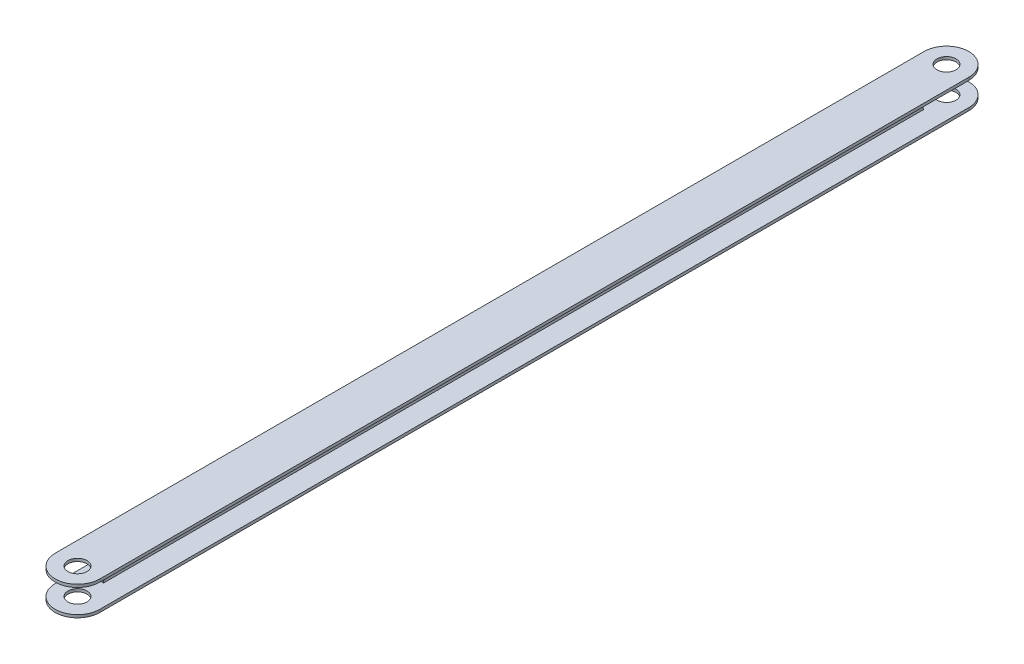
SolidWorks part; units mm, degrees
ref_plane "Front Plane" through (0, 0, 0) normal (0, 0, 1) x (1, 0, 0)
ref_plane "Top Plane" through (0, 0, 0) normal (0, 1, 0) x (1, 0, 0)
ref_plane "Right Plane" through (0, 0, 0) normal (1, 0, 0) x (0, 0, -1)
sketch "Sketch1" plane through (0, 0, 0) normal (0, 0, 1) x (1, 0, 0)
  line L0 (0, 0) -> (0, -5.6)
  line L1 (-0.6, 5) -> (0.6, 5)
  line L2 (-0.6, 5) -> (-0.6, -5)
  line L3 (-0.6, -5) -> (0.6, -5)
  line L4 (0.6, 5) -> (0.6, -5)
  line L5 (-0.6, 5) -> (0.6, -5) construction
  line L6 (-0.6, -5) -> (0.6, 5) construction
  line L7 (-9.5, -5) -> (9.5, -5)
  line L8 (-9.5, -5) -> (-9.5, -6.2)
  line L9 (-9.5, -6.2) -> (9.5, -6.2)
  line L10 (9.5, -5) -> (9.5, -6.2)
  line L11 (-9.5, -5) -> (9.5, -6.2) construction
  line L12 (-9.5, -6.2) -> (9.5, -5) construction
  line L13 (0, 0) -> (6.3315, 0) construction
  line L14 (-9.5, 6.2) -> (9.5, 5) construction
  line L15 (-9.5, 5) -> (9.5, 6.2) construction
  line L16 (9.5, 5) -> (9.5, 6.2)
  line L17 (-9.5, 6.2) -> (9.5, 6.2)
  line L18 (-9.5, 5) -> (-9.5, 6.2)
  line L19 (-9.5, 5) -> (9.5, 5)
  line L20 (-0.6, 5) -> (0.6, 5)
  point P0 (0, 0)
  point P6 (0, -5.6)
  point P19 (0, 5.6)
  dimension "D1" = 10
  dimension "D2" = 1.2
  dimension "D3" = 19
  dimension "D4" = 1.2
extrude "Boss-Extrude1" add sketch "Sketch1" along normal blind 389
sketch "Sketch3" plane through (0, 6.2, 0) normal (0, 1, 0) x (1, 0, 0)
  line L0 (-9.5, 0) -> (9.5, 0) construction
  line L1 (-14.5, -9.5) -> (-9.5, -9.5)
  line L2 (9.5, -9.5) -> (14.5, -9.5)
  line L3 (9.5, -389) -> (9.5, 0) construction
  line L4 (-9.5, -389) -> (-9.5, 0) construction
  line L12 (9.5, -9.5) -> (4.05, -9.5)
  line L13 (-4.05, -9.5) -> (-9.5, -9.5)
  line L16 (-19.5, -399) -> (19.5, -399)
  line L17 (19.5, -399) -> (19.5, 10)
  line L18 (19.5, 10) -> (-19.5, 10)
  line L19 (-19.5, 10) -> (-19.5, -399)
  line L20 (-19.5, -399) -> (19.5, -399)
  line L21 (19.5, -399) -> (19.5, 10)
  line L22 (19.5, 10) -> (-19.5, 10)
  line L23 (-19.5, 10) -> (-19.5, -399)
  arc A0 (9.5, -9.5) -> (-9.5, -9.5) centre (0, -9.5) ccw
  circle A1 centre (0, -9.5) radius 4.05
  arc A2 (14.5, -9.5) -> (-14.5, -9.5) centre (0, -9.5) ccw
  line M5 (9.5, 0) -> (-9.5, 0)
  line M6 (-9.5, 0) -> (-9.5, -389)
  line M8 (9.5, -389) -> (9.5, 0)
  dimension "D1" = 9.5
  dimension "D2" = 10
  dimension "D4" = 8.1
  dimension "D3" = 5
ref_plane "Plane4" through (0, 0, 194.5) normal (0, 0, 1) x (1, 0, 0)
extrude "Cut-Extrude2" cut sketch "Sketch3" along direction (0, 1, 0) on the side against the normal blind 370 contours A0 M5 M6 | A0 M8 M5 | L2 A2 L1 M6 M5 M8 | A1
mirror "Mirror1" about plane through (0, 0, 194.5) normal (0, 0, 1) of "Cut-Extrude2"
sketch "Sketch6" plane through (-0.6, 0, 0) normal (-1, 0, 0) x (0, 0, 1)
  line L0 (379.5, -5) -> (9.5, -5) construction
  line L1 (20, -5) -> (-1, -5)
  line L2 (20, -5) -> (20, -4.5176)
  line L3 (20, 5) -> (-1, 5)
  line L4 (-1, -5) -> (-1, 5)
  line L5 (20, -5) -> (-1, 5) construction
  line L6 (20, 5) -> (-1, -5) construction
  line L7 (9.5, 5) -> (9.5, -5)
  line L8 (20, 4.5176) -> (20, 5)
  arc A4 (20.5715, -3.6141) -> (20.5715, 3.6141) centre (18.8573, 0) ccw
  arc A5 (20, -4.5176) -> (20.5715, -3.6141) centre (21, -4.5176) cw
  arc A6 (20.5715, 3.6141) -> (20, 4.5176) centre (21, 4.5176) cw
  point P0 (9.5, 0)
  point P14 (22.8573, 0)
  point P20 (20, 3.8333)
  point P21 (0, 0)
  dimension "D2" = 1
  dimension "D3" = 4
  dimension "D1" = 21
extrude "Cut-Extrude4" cut sketch "Sketch6" along direction (1, 0, 0) on the side against the normal blind 370
mirror "Mirror2" about plane through (0, 0, 194.5) normal (0, 0, 1) of "Cut-Extrude4"
